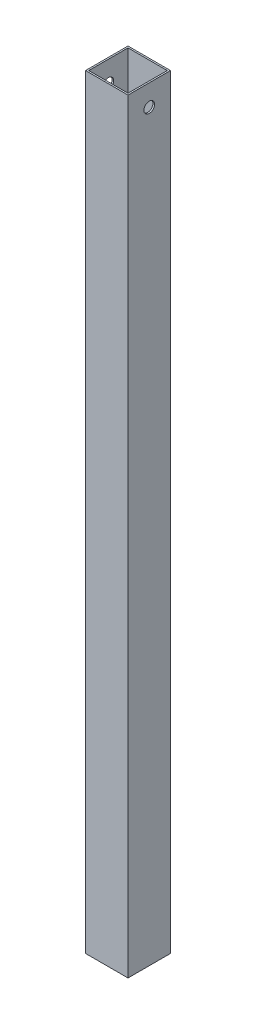
SolidWorks part; units mm, degrees
material "6061-T6 (SS)"
ref_plane "Front Plane" through (0, 0, 0) normal (0, 0, 1) x (1, 0, 0)
ref_plane "Top Plane" through (0, 0, 0) normal (0, 1, 0) x (1, 0, 0)
ref_plane "Right Plane" through (0, 0, 0) normal (1, 0, 0) x (0, 0, -1)
sketch "Sketch1" plane through (0, 0, 0) normal (0, 1, 0) x (1, 0, 0)
  line L0 (-11.7348, -11.7348) -> (11.7348, -11.7348)
  line L1 (-12.7, 12.7) -> (12.7, 12.7)
  line L2 (-12.7, 12.7) -> (-12.7, -12.7)
  line L3 (-12.7, -12.7) -> (12.7, -12.7)
  line L4 (12.7, 12.7) -> (12.7, -12.7)
  line L5 (-12.7, 12.7) -> (12.7, -12.7) construction
  line L6 (-12.7, -12.7) -> (12.7, 12.7) construction
  line L7 (11.7348, 11.7348) -> (11.7348, -11.7348)
  line L8 (-11.7348, 11.7348) -> (11.7348, 11.7348)
  line L9 (-11.7348, 11.7348) -> (-11.7348, -11.7348)
  point P0 (0, 0)
  dimension "D1" = 25.4
  dimension "D2" = 25.4
  dimension "D3" = 0.9652
extrude "Boss-Extrude1" add sketch "Sketch1" along normal blind 457.2
sketch "Sketch2" plane through (12.7, 0, 0) normal (1, 0, 0) x (0, 0, -1)
  line L0 (12.7, 457.2) -> (12.7, 0) construction
  line L2 (-12.7, 457.2) -> (12.7, 457.2) construction
  circle A0 centre (0, 444.5) radius 3.175
  dimension "D1" = 12.7
  dimension "D3" = 6.35
  dimension "D2" = 12.7
extrude "Cut-Extrude1" cut sketch "Sketch2" against normal through all
